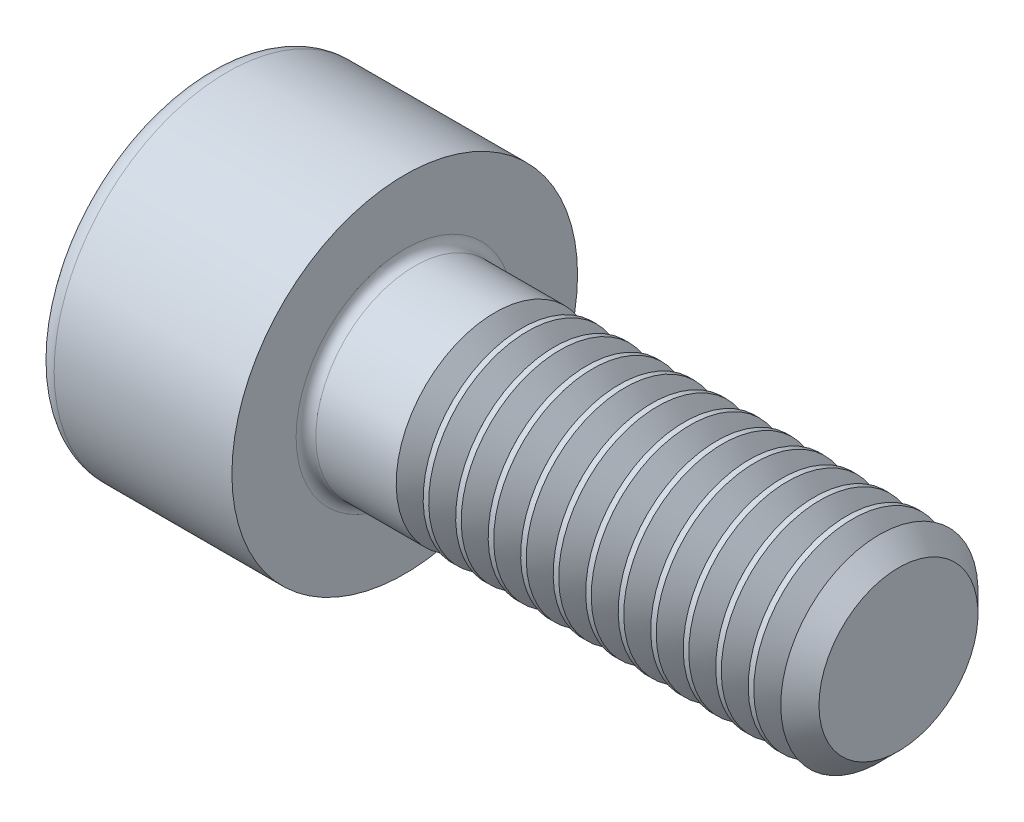
SolidWorks part; units mm, degrees
revolve "Base-Revolve" add sketch "BodySke"
sketch "BodySke" plane through (0, 0, 0) normal (0, 0, 1) x (1, 0, 0)
  line L0 (0, 0) -> (0, 3.5)
  line L1 (0, 3.5) -> (4, 3.5)
  line L2 (4, 3.5) -> (4, 2)
  line L3 (4, 2) -> (13.61, 2)
  line L4 (14, 1.61) -> (14, 0)
  line L5 (14, 0) -> (0, 0)
  line L6 (-31.75, 0) -> (127, 0) construction
  line L8 (14, 1.61) -> (13.61, 2)
  line L10 (14, -1.61) -> (13.61, -2) construction
  line L11 (4.7, 9.525) -> (4.7, 3.175) construction
  line L12 (4, 9.525) -> (4, 3.175) construction
  line L13 (-46, 9.525) -> (-46, 3.175) construction
cosmetic thread "ThreadCosmetic" [suppressed]
fillet "Fillet1" radius 0.2 1 edges at (4, 0, 2)
fillet "Fillet2" radius 0.4 1 edges at (0, 0, 3.5)
ref_plane "Plane1" through (0, 0, 0) normal (0, 0, 1) x (1, 0, 0)
ref_plane "Plane2" through (0, 0, 0) normal (0, 1, 0) x (1, 0, 0)
ref_plane "Plane3" through (0, 0, 0) normal (1, 0, 0) x (0, 0, -1)
sketch "Sketch2" plane through (0, 0, 0) normal (0, 0, 1) x (1, 0, 0)
  line L0 (0, 1.51) -> (2, 1.51)
  line L1 (2, 1.51) -> (2.8718, 0)
  line L2 (-31.75, 0) -> (127, 0) construction
  line L3 (2.8718, 0) -> (0, 0)
  line L4 (0, 0) -> (0, 1.51)
  line L6 (0, 0) -> (47.625, 0) construction
revolve "Hex-PreBroach" cut sketch "Sketch2" angle 360 about L6
sketch "Sketch3" plane through (0, 0, 0) normal (-1, 0, 0) x (0, 0.5, 0.866)
  line L0 (0.8718, 1.51) -> (-0.8718, 1.51)
  line L1 (-0.8718, 1.51) -> (-1.7436, 0)
  line L2 (0.8718, 1.51) -> (1.7436, 0)
  line L3 (0.8718, -1.51) -> (1.7436, 0)
  line L4 (0.8718, -1.51) -> (-0.8718, -1.51)
  line L5 (-0.8718, -1.51) -> (-1.7436, 0)
extrude "Hex" cut sketch "Sketch3" against normal blind 2
sketch "ThdSchSke" plane through (0, 0, 0) normal (0, 0, 1) x (1, 0, 0)
  line L0 (6.1, -1.61) -> (5.8269, -2)
  line L1 (6.1, -1.61) -> (6.3731, -2)
  line L2 (6.3731, -2) -> (6.3731, -2.5)
  line L3 (-3.175, 0) -> (5.1513, 0) construction
  line L4 (0, 3.1) -> (0, -3.1) construction
  line L5 (6.3731, -2.5) -> (5.8269, -2.5)
  line L6 (5.8269, -2.5) -> (5.8269, -2)
revolve "ThreadSchematic" cut sketch "ThdSchSke" angle 360 about L3
pattern_linear "ThdSchPat" count 12 spacing 0.6583 along (1, 0, 0) of "ThreadSchematic"
equation "\"D2@Sketch3\" = \"Hex_size@Sketch3\" / 2"
equation "\"D1@Sketch3\" = \"Hex_size@Sketch3\" / 2"
equation "\"D1@Sketch2\" = \"Hex_size@Sketch3\" / 2"
equation "\"Thread_minor@ThreadCosmetic\"  =  \"Minor_dia@BodySke\""
equation "\"Depth@Sketch2\" =  \"Key_eng@Hex\""
equation "\"Thread_length@ThreadCosmetic\" = ((sgn( (\"Length@BodySke\" - \"Advance@BodySke\" * 3.0) - \"Thread_nom@BodySke\" )-1)*( (\"Length@BodySke\" - \"Advance@BodySke\" * 3.0) - \"Thread_nom@BodySke\" ))/-2+ \"Thread_nom@BodySke\""
equation "\"Thread_minor@ThdSchSke\" = \"Minor_dia@BodySke\""
equation "\"Diameter@ThdSchSke\" = \"Diameter@BodySke\""
equation "\"Overcut@ThdSchSke\" = \"Diameter@BodySke\" * 1.25"
equation "\"Start@ThdSchSke\" = \"Head_ht@BodySke\" + \"Length@BodySke\" - \"Thread_length@ThreadCosmetic\"  '---Non-countersunk---"
equation "\"Num_threads@ThdSchPat\" = int( \"Thread_length@ThreadCosmetic\" / \"Advance@BodySke\" + 0.999 )  + 1"
equation "\"Advance@ThdSchPat\" = \"Thread_length@ThreadCosmetic\" /  (\"Num_threads@ThdSchPat\" - 1) 'relax it"
equation "\"Num_threads@ThdSchPat\" = \"Num_threads@ThdSchPat\" - sgn( \"Num_threads@ThdSchPat\" - 1) '---chamfered tips only---"
